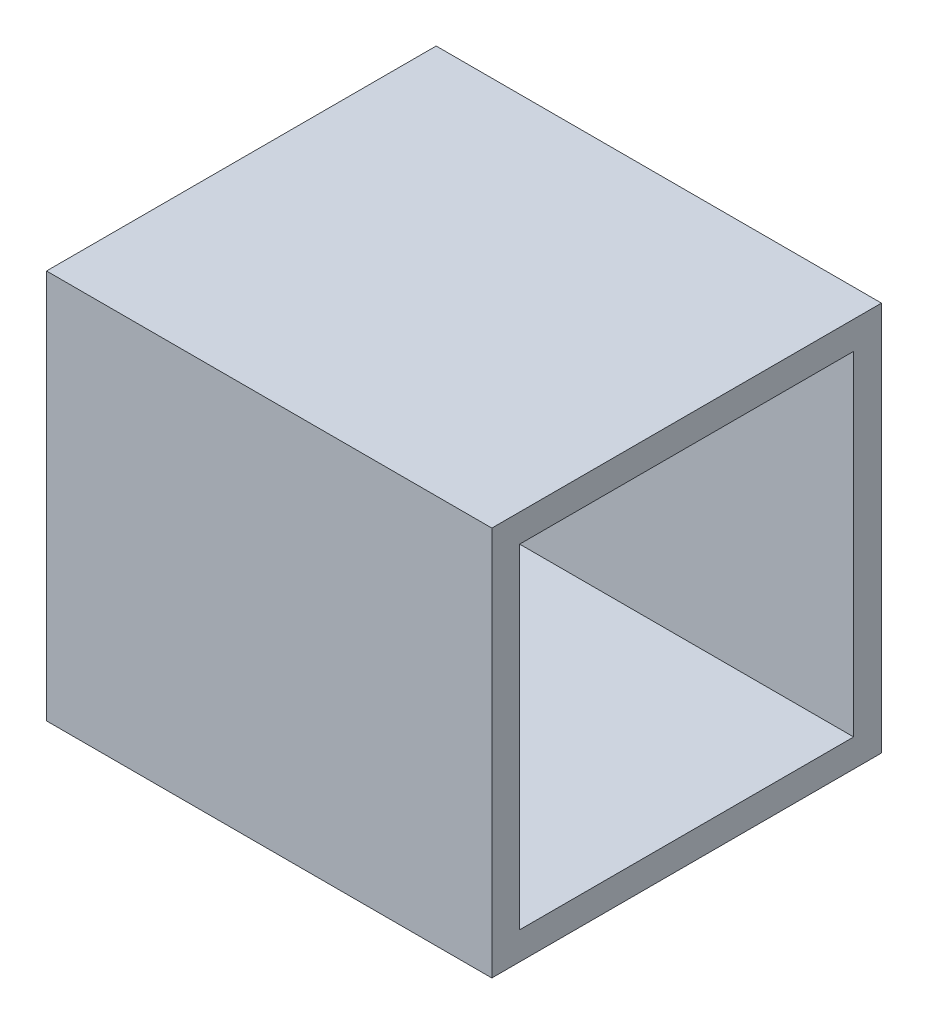
SolidWorks part; units mm, degrees
ref_plane "Front Plane" through (0, 0, 0) normal (0, 0, 1) x (1, 0, 0)
ref_plane "Top Plane" through (0, 0, 0) normal (0, 1, 0) x (1, 0, 0)
ref_plane "Right Plane" through (0, 0, 0) normal (1, 0, 0) x (0, 0, -1)
sketch "Sketch1" plane through (0, 0, 0) normal (0, 1, 0) x (1, 0, 0)
  line L1 (0, 0) -> (0.8, 0)
  line L2 (0, 0) -> (0, -0.7)
  line L3 (0, -0.7) -> (0.8, -0.7)
  line L4 (0.8, 0) -> (0.8, -0.7)
  point P4 (0, 0)
  dimension "D1" = 0.8
  dimension "D2" = 0.7
extrude "Boss-Extrude1" add sketch "Sketch1" along normal blind 0.7
sketch "Sketch2" plane through (0.8, 0, 0) normal (1, 0, 0) x (0, 0, -1)
  line L0 (-0.7, 0.7) -> (0, 0.7) construction
  line L1 (-0.65, 0.65) -> (-0.05, 0.65)
  line L2 (-0.65, 0.65) -> (-0.65, 0.05)
  line L3 (-0.65, 0.05) -> (-0.05, 0.05)
  line L4 (-0.05, 0.65) -> (-0.05, 0.05)
  line L5 (0, 0.7) -> (0, 0) construction
  point P6 (-0.35, 0.7)
  point P7 (-0.35, 0.65)
  point P10 (0, 0.35)
  point P11 (-0.05, 0.35)
  dimension "D1" = 0.6
  dimension "D2" = 0.6
extrude "Cut-Extrude1" cut sketch "Sketch2" against normal through all both and the other way through all
